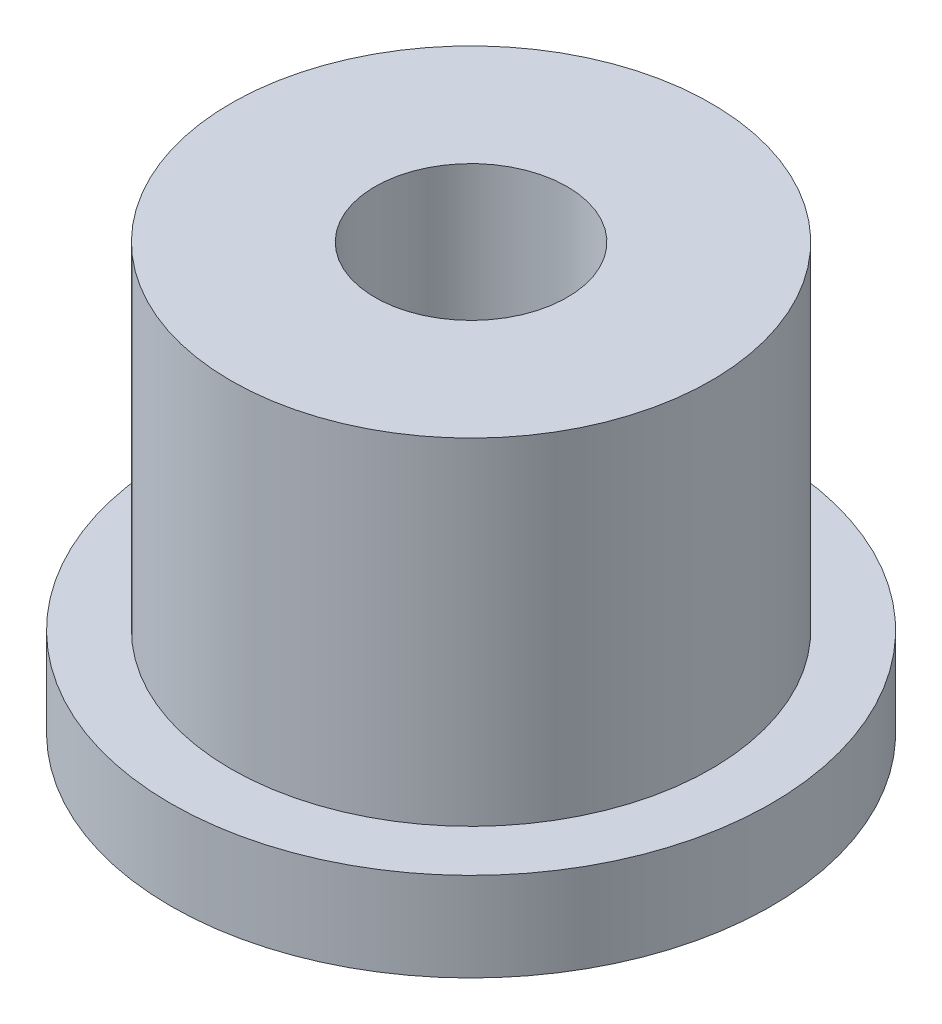
SolidWorks part; units mm, degrees
ref_plane "Front Plane" through (0, 0, 0) normal (0, 0, 1) x (1, 0, 0)
ref_plane "Top Plane" through (0, 0, 0) normal (0, 1, 0) x (1, 0, 0)
ref_plane "Right Plane" through (0, 0, 0) normal (1, 0, 0) x (0, 0, -1)
sketch "Sketch1" plane through (0, 0, 0) normal (0, 1, 0) x (1, 0, 0)
  circle A0 centre (0, 0) radius 5
  dimension "D1" = 10
extrude "Boss-Extrude1" add sketch "Sketch1" along normal blind 1.48
sketch "Sketch2" plane through (0, 1.48, 0) normal (0, 1, 0) x (1, 0, 0)
  circle A0 centre (0, 0) radius 4
  dimension "D1" = 8
extrude "Boss-Extrude2" add sketch "Sketch2" along normal blind 5.6
sketch "Sketch3" plane through (0, 0, 0) normal (0, -1, 0) x (1, 0, 0)
  circle A0 centre (0, 0) radius 1.6
  dimension "D1" = 3.2
extrude "Cut-Extrude1" cut sketch "Sketch3" against normal through all
sketch "Sketch4" plane through (0, 0, 0) normal (0, -1, 0) x (1, 0, 0)
  circle A0 centre (0, 0) radius 3
  dimension "D1" = 6
extrude "Cut-Extrude2" cut sketch "Sketch4" against normal blind 2
